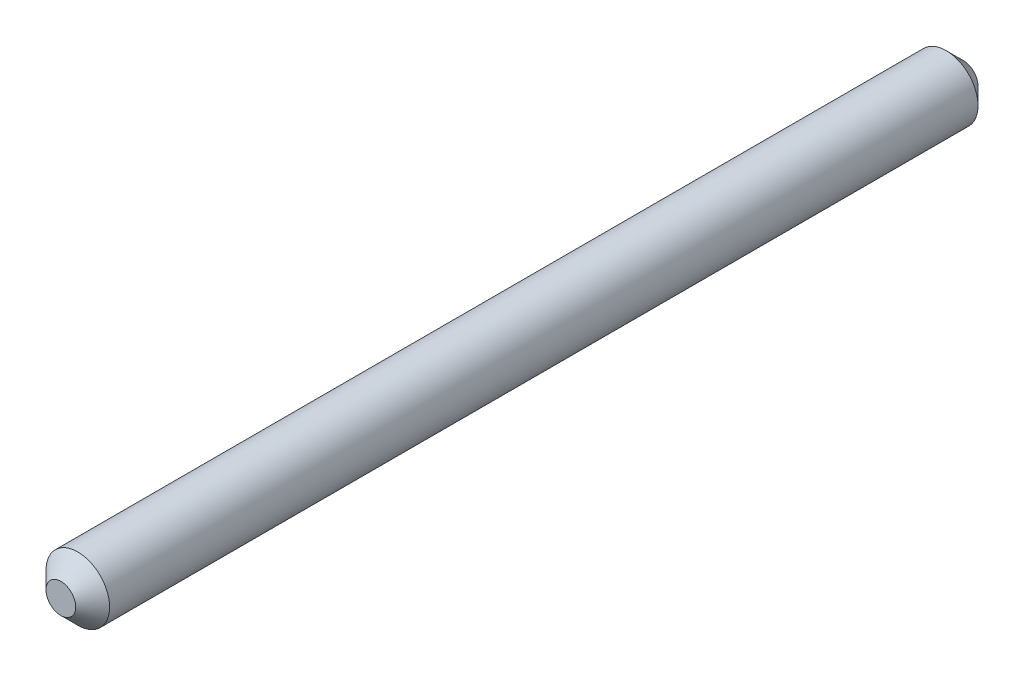
SolidWorks part; units mm, degrees
ref_plane "Front Plane" through (0, 0, 0) normal (0, 0, 1) x (1, 0, 0)
ref_plane "Top Plane" through (0, 0, 0) normal (0, 1, 0) x (1, 0, 0)
ref_plane "Right Plane" through (0, 0, 0) normal (1, 0, 0) x (0, 0, -1)
sketch "Sketch1" plane through (0, 0, 0) normal (0, 0, 1) x (1, 0, 0)
  circle A0 centre (0, 0) radius 2.3813
  dimension "D1" = 4.7625
extrude "Boss-Extrude1" add sketch "Sketch1" against normal blind 67.564
chamfer "Chamfer1" distance 1.27 angle 45 2 edges at (2.3813, 0, -67.564) (2.3813, 0, 0)
